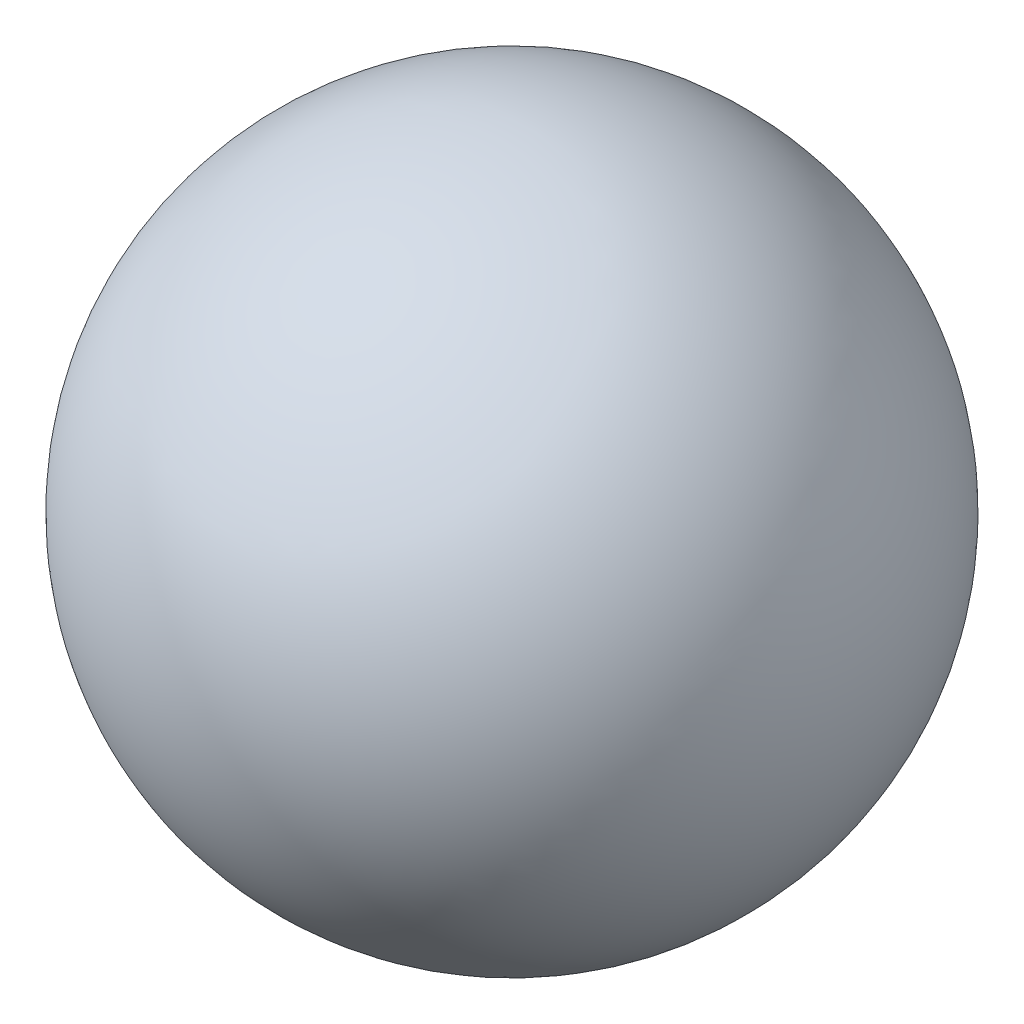
SolidWorks part; units mm, degrees
ref_plane "Front Plane" through (0, 0, 0) normal (0, 0, 1) x (1, 0, 0)
ref_plane "Top Plane" through (0, 0, 0) normal (0, 1, 0) x (1, 0, 0)
ref_plane "Right Plane" through (0, 0, 0) normal (1, 0, 0) x (0, 0, -1)
sketch "Sketch2" plane through (0, 0, 0) normal (0, 1, 0) x (1, 0, 0)
  line L0 (0, 1.5875) -> (0, -1.5875) construction
  line L1 (0, 1.5875) -> (0, -1.5875)
  arc A1 (0, 1.5875) -> (0, -1.5875) centre (0, 0) cw
revolve "Revolve11" add sketch "Sketch2" angle 360 about L0
